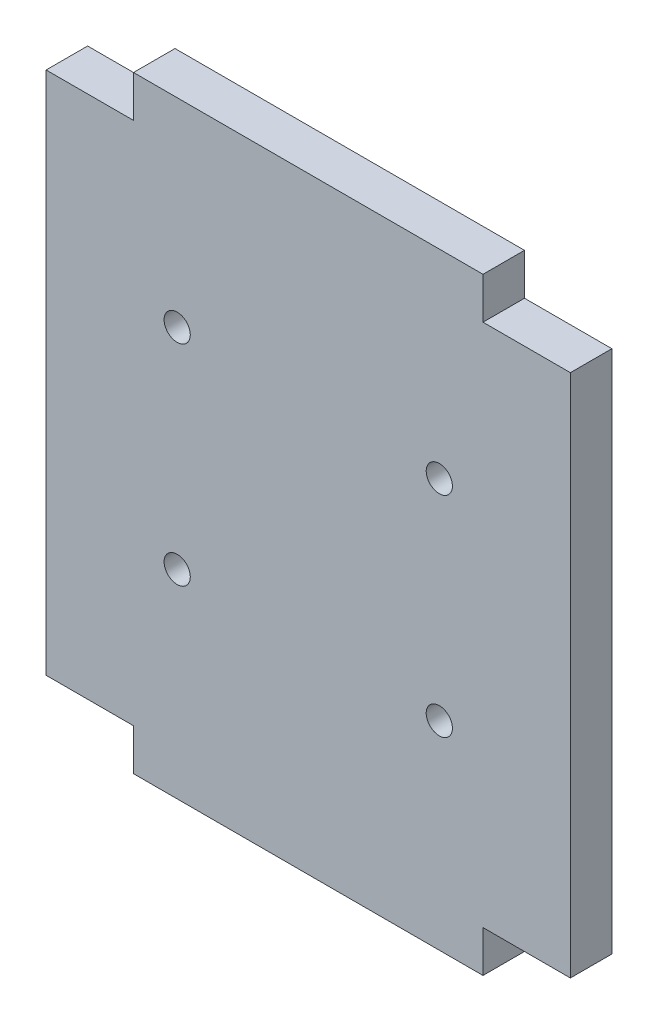
SolidWorks part; units mm, degrees
material "Pine"
ref_plane "Front Plane" through (0, 0, 0) normal (0, 0, 1) x (1, 0, 0)
ref_plane "Top Plane" through (0, 0, 0) normal (0, 1, 0) x (1, 0, 0)
ref_plane "Right Plane" through (0, 0, 0) normal (1, 0, 0) x (0, 0, -1)
sketch "Sketch1" plane through (0, 0, 0) normal (0, 0, 1) x (1, 0, 0)
  line L1 (-30, -34.75) -> (30, -34.75)
  line L2 (-30, -34.75) -> (-30, 34.75)
  line L3 (-30, 34.75) -> (30, 34.75)
  line L4 (30, -34.75) -> (30, 34.75)
  line L5 (-30, -34.75) -> (30, 34.75) construction
  line L6 (-30, 34.75) -> (30, -34.75) construction
  point P0 (0, 0)
  dimension "D1" = 69.5
  dimension "D2" = 60
extrude "Boss-Extrude1" add sketch "Sketch1" along normal blind 4.75
sketch "Sketch2" plane through (0, 0, 4.75) normal (0, 0, 1) x (1, 0, 0)
  line L0 (0, 0) -> (-30, 0) construction
  line L1 (-30, 34.75) -> (-20, 34.75)
  line L2 (-30, 34.75) -> (-30, 30)
  line L3 (-30, 30) -> (-20, 30)
  line L4 (-20, 34.75) -> (-20, 30)
  line L5 (-30, 34.75) -> (-30, -34.75) construction
  line L6 (-30, 0) -> (0, 0) construction
  line L7 (0, 0) -> (0, 34.75) construction
  line L8 (30, 34.75) -> (-30, 34.75) construction
  line L9 (-30, -30) -> (-20, -30)
  line L10 (-20, -34.75) -> (-20, -30)
  line L11 (-30, -34.75) -> (-20, -34.75)
  line L12 (-30, -34.75) -> (-30, -30)
  line L13 (30, -34.75) -> (30, -30)
  line L14 (30, -34.75) -> (20, -34.75)
  line L15 (20, -34.75) -> (20, -30)
  line L16 (30, -30) -> (20, -30)
  line L17 (30, 30) -> (20, 30)
  line L18 (20, 34.75) -> (20, 30)
  line L19 (30, 34.75) -> (20, 34.75)
  line L20 (30, 34.75) -> (30, 30)
  dimension "D1" = 4.75
  dimension "D2" = 10
extrude "Cut-Extrude1" cut sketch "Sketch2" against normal through all both and the other way through all
sketch "Sketch3" plane through (0, 0, 4.75) normal (0, 0, 1) x (1, 0, 0)
  line L1 (-15, -12) -> (15, -12) construction
  line L2 (-15, -12) -> (-15, 12) construction
  line L3 (-15, 12) -> (15, 12) construction
  line L4 (15, -12) -> (15, 12) construction
  line L5 (-15, -12) -> (15, 12) construction
  line L6 (-15, 12) -> (15, -12) construction
  circle A0 centre (-15, 12) radius 1.5
  circle A1 centre (-15, -12) radius 1.5
  circle A2 centre (15, -12) radius 1.5
  circle A3 centre (15, 12) radius 1.5
  point P0 (0, 0)
  dimension "D3" = 3
  dimension "D1" = 30
  dimension "D2" = 24
extrude "Cut-Extrude2" cut sketch "Sketch3" against normal through all both
